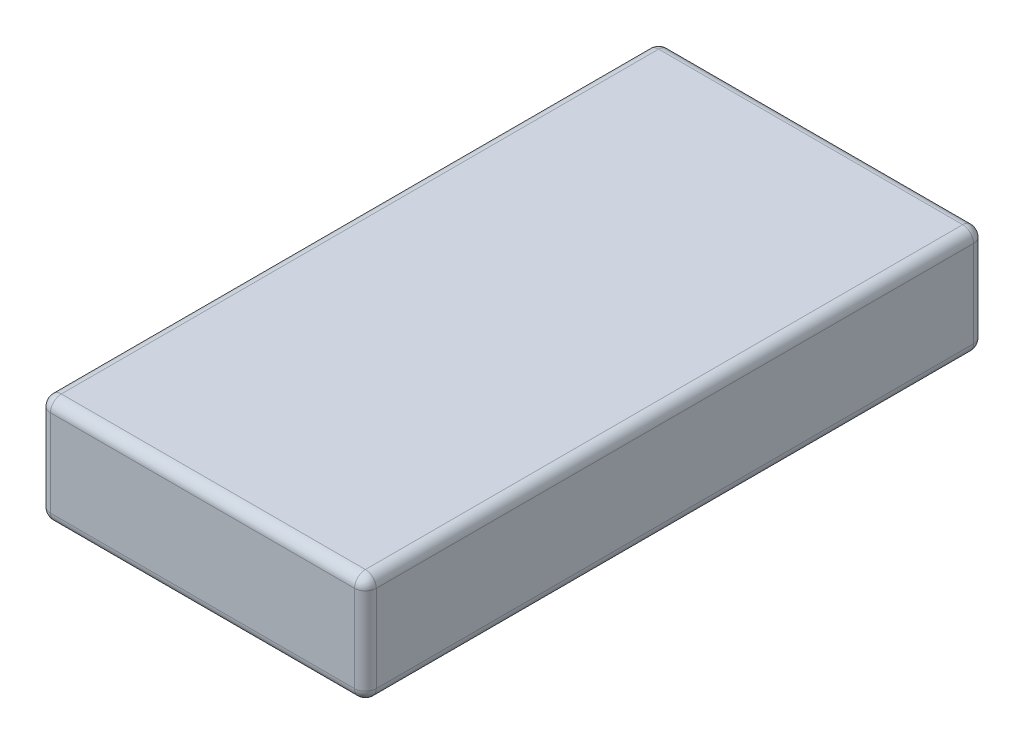
SolidWorks part; units mm, degrees
ref_plane "Front Plane" through (0, 0, 0) normal (0, 0, 1) x (1, 0, 0)
ref_plane "Top Plane" through (0, 0, 0) normal (0, 1, 0) x (1, 0, 0)
ref_plane "Right Plane" through (0, 0, 0) normal (1, 0, 0) x (0, 0, -1)
sketch "Sketch1" plane through (0, 0, 0) normal (0, 0, 1) x (1, 0, 0)
  line L1 (-15, 5) -> (15, 5)
  line L2 (-15, 5) -> (-15, -5)
  line L3 (-15, -5) -> (15, -5)
  line L4 (15, 5) -> (15, -5)
  line L5 (-15, 5) -> (15, -5) construction
  line L6 (-15, -5) -> (15, 5) construction
  point P0 (0, 0)
  dimension "D1" = 10
  dimension "D2" = 30
extrude "Boss-Extrude1" add sketch "Sketch1" along normal blind 57
fillet "Fillet1" radius 1 12 edges at (15, 0, 0) (0, 5, 0) (15, 0, 57) (0, 5, 57) (-15, 0, 57) (0, -5, 57) (15, -5, 28.5) (-15, 5, 28.5) (15, 5, 28.5) (-15, -5, 28.5) (0, -5, 0) (-15, 0, 0)
